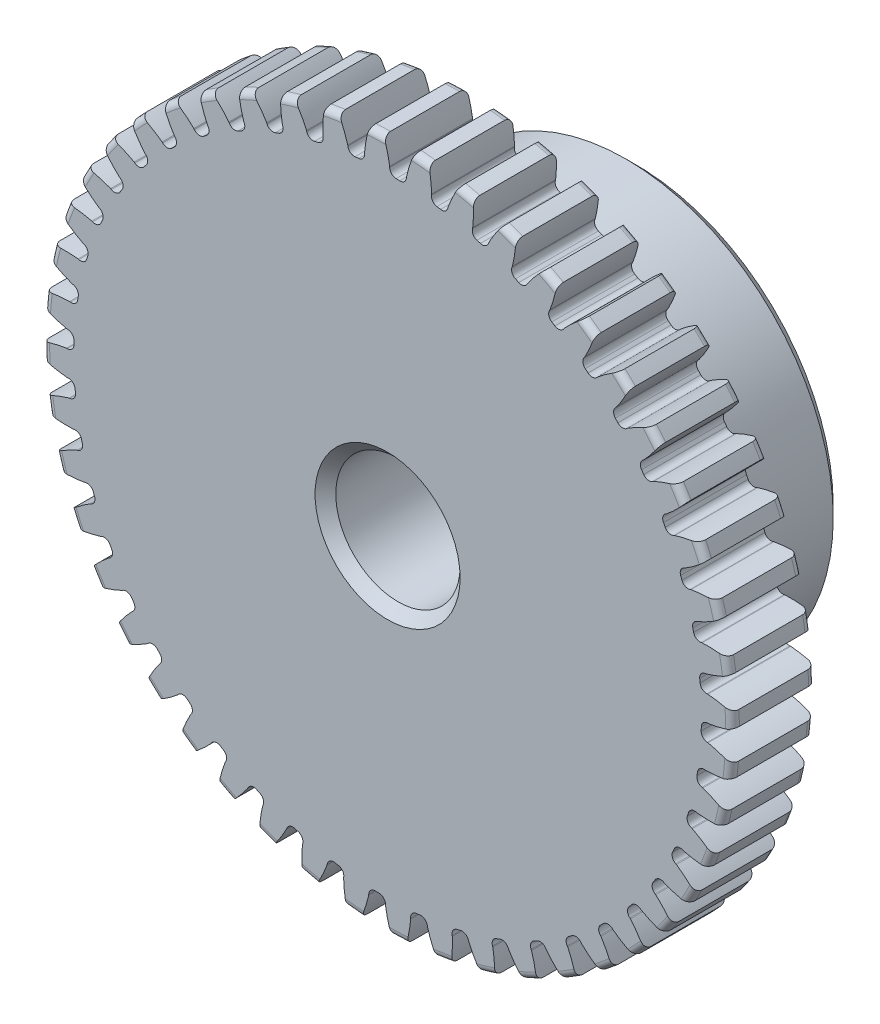
SolidWorks part; units mm, degrees
ref_plane "Front" through (0, 0, 0) normal (0, 0, 1) x (1, 0, 0)
ref_plane "Top" through (0, 0, 0) normal (0, 1, 0) x (1, 0, 0)
ref_plane "Right" through (0, 0, 0) normal (1, 0, 0) x (0, 0, -1)
sketch "Sketch1" plane through (0, 0, 0) normal (0, 0, 1) x (1, 0, 0)
  line L0 (-609.6, 0) -> (609.6, 0) construction
  circle A0 centre (0, 0) radius 13.208
  circle A1 centre (0, 0) radius 12.7 construction
  circle A3 centre (0, 0) radius 12.0174 construction
  dimension "D1" = 1.1906
  dimension "OD" = 26.416
  dimension "Ptich Dia" = 25.4
  dimension "Root Dia" = 24.0347
  dimension "D3" = 0.508
  dimension "Number of Teeth" = 1219.2
extrude "Boss-Extrude1" add sketch "Sketch1" against normal blind 3.175
sketch "Sketch2" plane through (0, 0, 0) normal (1, 0, 0) x (0, 0, -1)
  line L0 (3.175, 0) -> (9.525, 0)
  line L1 (3.175, 0) -> (3.175, 7.9375)
  line L2 (3.175, 7.9375) -> (9.525, 7.9375)
  line L3 (9.525, 7.9375) -> (9.525, 0)
  point P5 (9.525, -7.9375)
  point P6 (0, -13.208)
  point P7 (3.175, -13.208)
  point P9 (0, 13.208)
  dimension "Face Wd" = 3.175
  dimension "B Hub Dia" = 15.875
  dimension "D O'all Lg." = 9.525
revolve "Revolve1" add sketch "Sketch2" angle 360 about L0
fillet "Fillet2" radius 0.2642 3 edges at (13.208, 0, -3.175) (13.208, 0, 0) (7.9375, 0, -3.175)
sketch "Sketch3" plane through (0, 0, 0) normal (0, 0, 1) x (1, 0, 0)
  line L0 (0, 0) -> (0, 13.208) construction
  line L1 (-3.0785, 11.9038) -> (0, 12.7)
  line L2 (-9.5921, 12.7) -> (9.5921, 12.7) construction
  line L3 (-9.2865, 10.2983) -> (9.2865, 15.1017) construction
  line L4 (-3.0785, 11.9038) -> (0, 0) construction
  line L5 (-7.8523, 9.4615) -> (0, 0) construction
  line L6 (-7.8523, 9.4615) -> (-1.2652, 14.9283) construction
  line L7 (-2.1466, 12.1066) -> (0, 0) construction
  line L8 (-2.1466, 12.1066) -> (0.045, 12.4952) construction
  arc A0 (-3.0785, 11.9038) -> (-7.8523, 9.4615) centre (0, 0) ccw
  circle A1 centre (0, 0) radius 12.7 construction
  circle A2 centre (0, 0) radius 12.2955 construction
  arc A3 (-3.0785, 11.9038) -> (-2.1466, 12.1066) centre (0, 0) cw
  circle A4 centre (0, 0) radius 13.208 construction
  point P6 (0, 12.7)
  dimension "D1" = 3.1798
  dimension "Pressure Angle" = 14.5
  dimension "D2" = 5.4057
  dimension "D3" = 8.5601
  dimension "D4" = 0.9539
  dimension "D5" = 2.2259
sketch "Sketch4" plane through (0, 0, 0) normal (0, 0, 1) x (1, 0, 0)
  line L0 (0, 0) -> (0.4153, 12.6864) construction
  line L1 (0.0798, 12.2952) -> (0.0798, 12.0171)
  line L2 (0, 12.7) -> (0.8306, 12.6728) construction
  line L3 (0.7245, 12.2741) -> (0.7063, 11.9966)
  line L4 (0.0798, 12.0171) -> (0, 0) construction
  line L5 (0, 0) -> (0, 13.208) construction
  line L6 (-7.8523, 9.4615) -> (-1.2652, 14.9283) construction
  line L7 (-7.8523, 9.4615) -> (-1.2652, 14.9283) construction
  arc A0 (0.7063, 11.9966) -> (0.0798, 12.0171) centre (0, 0) ccw
  arc A1 (0, 12.7) -> (0.8306, 12.6728) centre (0, 0) cw construction
  circle A2 centre (0, 0) radius 12.7 construction
  circle A3 centre (0, 0) radius 12.2955 construction
  circle A4 centre (0, 0) radius 12.0174 construction
  arc A5 (2.2389, 14.8136) -> (-1.2652, 14.9283) centre (0, 0) ccw
  spline S0 degree 2 poles (-1.2652, 14.9283) (-0.1435, 13.7672) (0.0798, 12.2952) knots 0 0 0 1 1 1
  spline S1 degree 2 poles (2.2389, 14.8136) (1.0436, 13.7283) (0.7245, 12.2741) knots 0 0 0 1 1 1
  dimension "D1" = 0.8312
extrude "Cut-Extrude1" cut sketch "Sketch4" against normal through all
fillet "Fillet1" radius 0.2494 2 edges at (0.7063, 11.9966, -1.5875) (0.0798, 12.0171, -1.5875)
pattern_circular "CirPattern1" count 48 over 360 about axis through (0, 0, -3.175) along (0, 0, 1) of "Cut-Extrude1", "Fillet1"
sketch "Sketch5" plane through (0, 0, 0) normal (0, 0, 1) x (1, 0, 0)
  circle A0 centre (0, 0) radius 2.3813
  circle A1 centre (0, 0) radius 1.5875 construction
  dimension "Bore Min" = 4.7625
  dimension "Bore Max" = 3.175
extrude "Cut-Extrude2" cut sketch "Sketch5" against normal through all
chamfer "Chamfer1" distance 0.3969 angle 45 3 edges at (7.9375, 0, -9.525) (2.3813, 0, 0) (2.3813, 0, -9.525)
sketch "Pitch Dia" plane through (0, 0, 0) normal (0, 0, 1) x (1, 0, 0)
  circle A0 centre (0, 0) radius 12.7 construction
  circle A1 centre (0, 0) radius 12.7 construction
equation "\"D1@Boss-Extrude1\" = \"Face Wd@Sketch2\""
equation "\"D2@Sketch3\" = \"D1@Sketch3\"*1.7"
equation "\"D3@Sketch3\" = \"D1@Sketch3\"+\"D2@Sketch3\"-.001"
equation "\"D4@Sketch3\" = \"D1@Sketch3\"*.3"
equation "\"D5@Sketch3\" = \"D1@Sketch3\"-\"D4@Sketch3\""
equation "\"D1@Sketch4\" = 1.5708/(\"Number of Teeth@Sketch1\"/\"Ptich Dia@Sketch1\")"
equation "\"D1@Chamfer1\" = \"B Hub Dia@Sketch2\"*.025"
equation "\"D1@CirPattern1\" = \"Number of Teeth@Sketch1\""
equation "\"D1@Fillet1\" = \"D1@Sketch4\"*.3"
equation "\"D1@Fillet2\" = \"OD@Sketch1\"*.01"
equation "\"D1@Sketch1\" = 2.250/(\"Number of Teeth@Sketch1\"/\"Ptich Dia@Sketch1\")"
